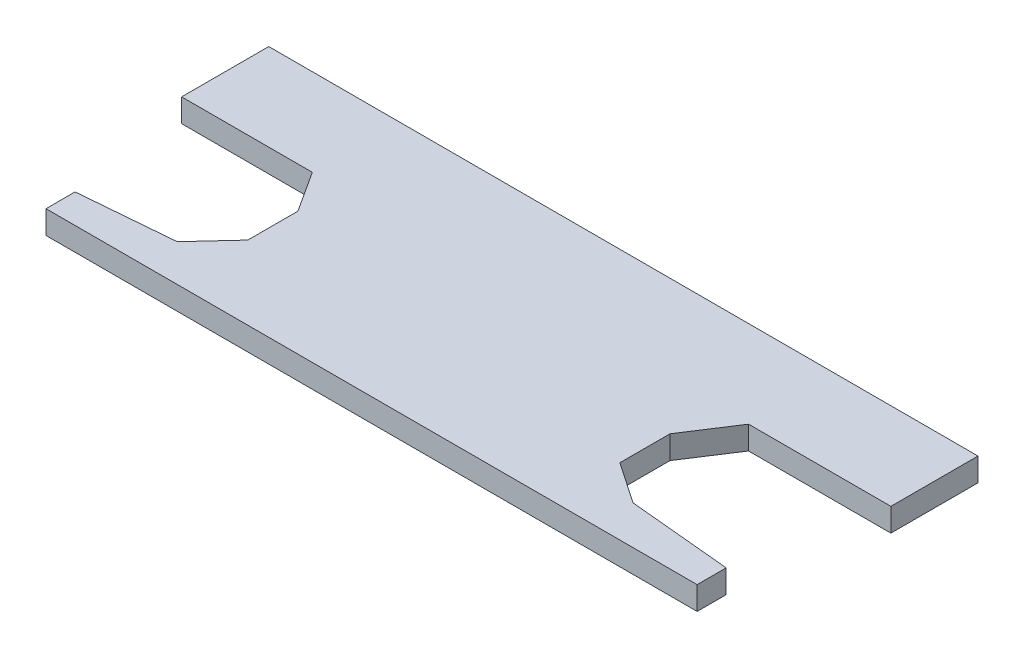
SolidWorks part; units mm, degrees
ref_plane "Front Plane" through (0, 0, 0) normal (0, 0, 1) x (1, 0, 0)
ref_plane "Top Plane" through (0, 0, 0) normal (0, 1, 0) x (1, 0, 0)
ref_plane "Right Plane" through (0, 0, 0) normal (1, 0, 0) x (0, 0, -1)
sketch "Sketch1" plane through (0, 0, 0) normal (0, 1, 0) x (1, 0, 0)
  line L1 (0, 0) -> (48.84, 0)
  line L2 (0, 0) -> (0, 17.34)
  line L3 (0, 17.34) -> (48.84, 17.34)
  line L4 (48.84, 0) -> (48.84, 17.34)
  dimension "D1" = 48.84
  dimension "D2" = 17.34
extrude "main square" add sketch "Sketch1" along normal blind 1.6
sketch "Sketch2" plane through (0, 1.6, 0) normal (0, 1, 0) x (1, 0, 0)
  line L0 (0, 17.34) -> (0, 11.34)
  line L1 (0, 17.34) -> (0, 0) construction
  line L2 (0, 11.34) -> (9, 11.34)
  line L3 (48.84, 11.34) -> (39.04, 11.34)
  line L4 (48.84, 0) -> (48.84, 17.34) construction
  line L5 (39.04, 11.34) -> (36.91, 8.0611)
  line L6 (9, 11.34) -> (10.82, 8.5275)
  line L7 (10.82, 8.5275) -> (10.82, 5.0775)
  line L8 (36.91, 8.0611) -> (36.91, 4.6111)
  line L9 (36.91, 4.6111) -> (39.75, 2.67)
  line L10 (10.82, 5.0775) -> (8.4865, 2.55)
  line L11 (0, 0) -> (0, 2.5) construction
  line L12 (2, 0) -> (2, 2)
  line L13 (0, 0) -> (48.84, 0) construction
  line L14 (2, 2) -> (8.4865, 2.55)
  line L15 (46.84, 0) -> (46.84, 2)
  line L16 (39.75, 2.67) -> (46.84, 2)
  line L17 (2, 0) -> (0, 0)
  line L18 (0, 0) -> (0, 11.34)
  line L19 (46.84, 0) -> (48.84, 0)
  line L20 (48.84, 0) -> (48.84, 11.34)
  line M10 (0, 17.34) -> (0, 0)
  line M11 (0, 0) -> (48.84, 0)
  line M12 (48.84, 0) -> (48.84, 17.34)
  dimension "D1" = 6
  dimension "D2" = 9
  dimension "D3" = 9.8
  dimension "D4" = 3.91
  dimension "D5" = 3.35
  dimension "D6" = 3.45
  dimension "D7" = 3.45
  dimension "D8" = 3.44
  dimension "D9" = 3.44
  dimension "D10" = 2.5
  dimension "D11" = 11.93
  dimension "D12" = 10.82
  dimension "D13" = 2
  dimension "D14" = 2
  dimension "D15" = 2
  dimension "D16" = 2
  dimension "D17" = 2.55
  dimension "D18" = 2.67
extrude "servo holes" cut sketch "Sketch2" against normal blind 1.6 contours L9 L16 L15 L3 L5 L8 M11 M12 | L12 L14 L10 L7 L6 L2 L18 M10 M11
sketch "switch location" plane through (0, 1.6, 0) normal (0, 1, 0) x (1, 0, 0)
  line L0 (36.91, 8.0611) -> (36.91, 4.6111) construction
  line L2 (48.84, 17.34) -> (0, 17.34) construction
  line L3 (20.81, 11.74) -> (29.71, 11.74)
  line L4 (20.81, 11.74) -> (20.81, 8.09)
  line L5 (20.81, 8.09) -> (29.71, 8.09)
  line L6 (29.71, 11.74) -> (29.71, 8.09)
  line L7 (25.26, 11.74) -> (25.26, 8.09) construction
  line L8 (20.81, 9.915) -> (29.71, 9.915) construction
  dimension "D1" = 11.65
  dimension "D2" = 5.6
  dimension "D3" = 3.65
  dimension "D4" = 8.9
